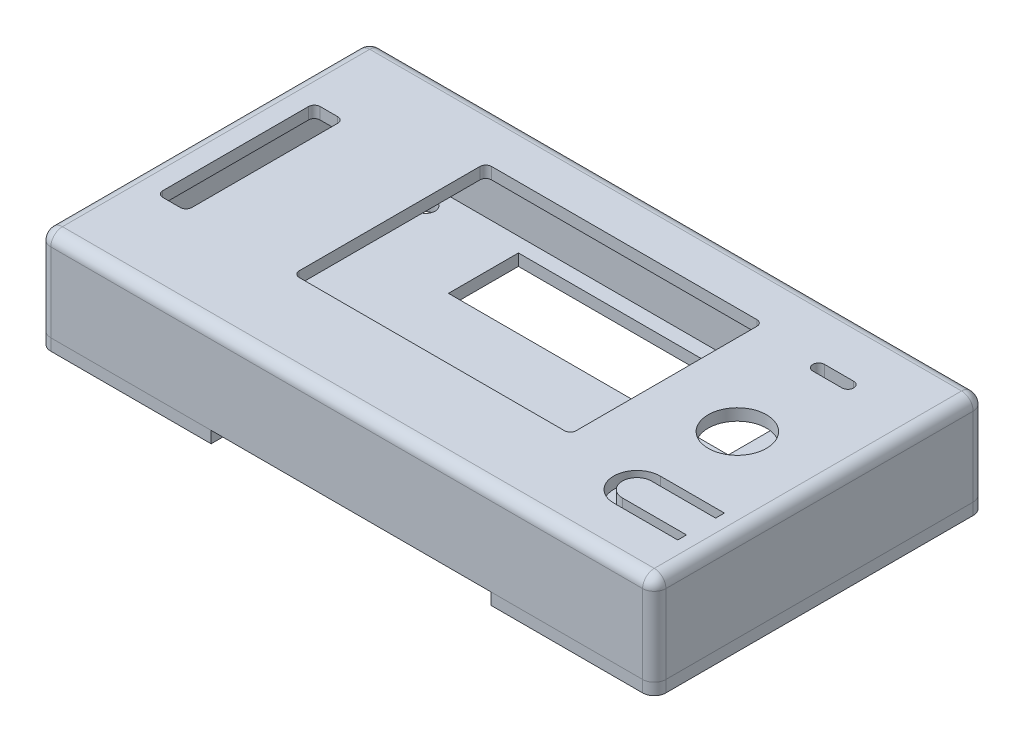
SolidWorks part; units mm, degrees
ref_plane "Alzado" through (0, 0, 0) normal (0, 0, 1) x (1, 0, 0)
ref_plane "Planta" through (0, 0, 0) normal (0, 1, 0) x (1, 0, 0)
ref_plane "Vista lateral" through (0, 0, 0) normal (1, 0, 0) x (0, 0, -1)
sketch "Croquis1" plane through (0, 0, 0) normal (0, 1, 0) x (1, 0, 0)
  line L0 (-2.25, 54.45) -> (103.25, 54.45)
  line L1 (0, 0) -> (101, 0) construction
  line L2 (0, 0) -> (0, 52.2) construction
  line L3 (0, 52.2) -> (101, 52.2) construction
  line L4 (101, 0) -> (101, 52.2) construction
  line L5 (26.6, 45.5) -> (74.1, 45.5)
  line L6 (26.6, 45.5) -> (26.6, 12.5)
  line L7 (26.6, 12.5) -> (74.1, 12.5)
  line L8 (74.1, 45.5) -> (74.1, 12.5)
  line L9 (3, 39.7) -> (8, 39.7)
  line L10 (3, 39.7) -> (3, 12.7)
  line L11 (3, 12.7) -> (8, 12.7)
  line L12 (8, 39.7) -> (8, 12.7)
  line L13 (103.25, -2.25) -> (103.25, 54.45)
  line L14 (-2.25, -2.25) -> (103.25, -2.25)
  line L15 (-2.25, -2.25) -> (-2.25, 54.45)
  line L16 (88.05, 12.48) -> (99.05, 12.48)
  line L17 (88.05, 7.48) -> (99.05, 7.48)
  line L18 (88.05, 5.98) -> (99.05, 5.98)
  line L19 (88.05, 13.98) -> (99.05, 13.98)
  line L20 (99.05, 13.98) -> (99.05, 12.48)
  line L21 (99.05, 7.48) -> (99.05, 5.98)
  line L22 (90.55, 43.65) -> (85.55, 43.65) construction
  line L23 (90.55, 42.65) -> (85.55, 42.65)
  line L24 (90.55, 44.65) -> (85.55, 44.65)
  line L25 (-0.75, -0.75) -> (101.75, -0.75) construction
  line L26 (101.75, -0.75) -> (101.75, 52.95) construction
  line L27 (-0.75, 52.95) -> (101.75, 52.95) construction
  line L28 (-0.75, -0.75) -> (-0.75, 52.95) construction
  circle A0 centre (98.3, 49.5) radius 1.6 construction
  circle A1 centre (98.3, 2.7) radius 1.6 construction
  circle A2 centre (12.3, 49.5) radius 1.6 construction
  circle A3 centre (12.3, 2.7) radius 1.6 construction
  circle A4 centre (88.05, 27.2) radius 5
  circle A5 centre (88.05, 43.65) radius 3 construction
  arc A6 (88.05, 12.48) -> (88.05, 7.48) centre (88.05, 9.98) ccw
  arc A7 (88.05, 13.98) -> (88.05, 5.98) centre (88.05, 9.98) ccw
  arc A8 (90.55, 42.65) -> (90.55, 44.65) centre (90.55, 43.65) ccw
  arc A9 (85.55, 44.65) -> (85.55, 42.65) centre (85.55, 43.65) ccw
  point P41 (88.05, 43.65)
  dimension "D3" = 3.2
  dimension "D6" = 2.7
  dimension "D12" = 10
  dimension "D15" = 6
  dimension "D17" = 5
  dimension "D1" = 52.2
  dimension "D2" = 101
  dimension "D4" = 46.8
  dimension "D5" = 2.7
  dimension "D7" = 86
  dimension "D8" = 47.5
  dimension "D9" = 33
  dimension "D10" = 12.5
  dimension "D11" = 26.9
  dimension "D13" = 12.95
  dimension "D14" = 25
  dimension "D16" = 8.55
  dimension "D18" = 17.22
  dimension "D19" = 27
  dimension "D20" = 5
  dimension "D21" = 12.5
  dimension "D22" = 8
  dimension "D24" = 11
  dimension "D25" = 1.5
  dimension "D26" = 5
  dimension "D27" = 2
  dimension "D23" = 1.5
  dimension "D28" = 0.75
extrude "Saliente-Extruir1" add sketch "Croquis1" along normal blind 2
sketch "Croquis5" plane through (0, 0, 0) normal (0, -1, 0) x (1, 0, 0)
  line L8 (-2.25, 2.25) -> (-2.25, -54.45) construction
  line L9 (-2.25, 2.25) -> (103.25, 2.25) construction
  line L10 (103.25, 2.25) -> (103.25, -54.45) construction
  line L11 (-2.25, -54.45) -> (103.25, -54.45) construction
  line L12 (-2.25, 2.25) -> (-2.25, -54.45)
  line L13 (-2.25, 2.25) -> (103.25, 2.25)
  line L14 (103.25, 2.25) -> (103.25, -54.45)
  line L15 (-2.25, -54.45) -> (103.25, -54.45)
  line L16 (101.75, 0.75) -> (101.75, -52.95) construction
  line L17 (-0.75, 0.75) -> (101.75, 0.75) construction
  line L18 (-0.75, 0.75) -> (-0.75, -52.95) construction
  line L19 (-0.75, -52.95) -> (101.75, -52.95) construction
  line L20 (101.75, 0.75) -> (101.75, -52.95)
  line L21 (-0.75, 0.75) -> (101.75, 0.75)
  line L22 (-0.75, 0.75) -> (-0.75, -52.95)
  line L23 (-0.75, -52.95) -> (101.75, -52.95)
extrude "Saliente-Extruir4" add sketch "Croquis5" along normal blind 13.5
sketch "Croquis6" plane through (0, -13.5, 0) normal (0, -1, 0) x (1, 0, 0)
  line L0 (103.25, 2.25) -> (103.25, -54.45) construction
  line L1 (-2.25, 2.25) -> (103.25, 2.25) construction
  line L2 (-2.25, 2.25) -> (-2.25, -54.45) construction
  line L3 (-2.25, -54.45) -> (103.25, -54.45) construction
  line L4 (103.25, 2.25) -> (103.25, -54.45)
  line L5 (-2.25, 2.25) -> (27.25, 2.25)
  line L6 (-2.25, 2.25) -> (-2.25, -54.45)
  line L7 (-2.25, -54.45) -> (103.25, -54.45)
  line L8 (50.5, 2.25) -> (50.5, -54.45) construction
  line L9 (-0.75, 0.75) -> (-0.75, -52.95) construction
  line L14 (9.45, -48.95) -> (2.45, -48.95)
  line L15 (9.45, -48.95) -> (9.45, -3.95)
  line L16 (9.45, -3.95) -> (2.45, -3.95)
  line L17 (2.45, -48.95) -> (2.45, -3.95)
  line L18 (-0.75, -52.95) -> (101.75, -52.95) construction
  line L19 (103.25, -26.1) -> (-2.25, -26.1) construction
  line L20 (75.25, -50.45) -> (27.25, -50.45)
  line L21 (75.25, -50.45) -> (75.25, -38.45)
  line L22 (75.25, -38.45) -> (27.25, -38.45)
  line L23 (27.25, -50.45) -> (27.25, -38.45)
  line L25 (75.25, 2.25) -> (75.25, -3.75)
  line L26 (75.25, -3.75) -> (27.25, -3.75)
  line L27 (27.25, 2.25) -> (27.25, -3.75)
  line L28 (75.25, 2.25) -> (103.25, 2.25)
  circle A0 centre (98.3, -2.7) radius 1.6 construction
  circle A1 centre (12.3, -49.5) radius 1.6 construction
  circle A2 centre (12.3, -49.5) radius 1.6
  circle A3 centre (98.3, -49.5) radius 1.6 construction
  circle A4 centre (98.3, -2.7) radius 1.6
  circle A7 centre (98.3, -49.5) radius 1.6
  circle A14 centre (12.3, -2.7) radius 1.6 construction
  circle A15 centre (12.3, -2.7) radius 1.6
  circle A16 centre (80.5, -26.1) radius 1.55
  circle A17 centre (20.5, -26.1) radius 1.55
  dimension "D5" = 48
  dimension "D11" = 3.1
  dimension "D1" = 45
  dimension "D2" = 7
  dimension "D3" = 3.2
  dimension "D4" = 4
  dimension "D6" = 12
  dimension "D7" = 2.5
  dimension "D8" = 28
  dimension "D9" = 48
  dimension "D10" = 6
  dimension "D12" = 30
extrude "Saliente-Extruir5" add sketch "Croquis6" along normal blind 2
ref_plane "Plano1" through (0, -13.5, 0) normal (0, -1, 0) x (-1, 0, 0)
sketch "Croquis8" plane through (0, 0, 0) normal (0, -1, 0) x (1, 0, 0)
  line L0 (0, 0) -> (101, 0) construction
  line L2 (9.225, 0.75) -> (9.225, -6.25)
  line L3 (9.225, -6.25) -> (15.375, -6.25)
  line L4 (15.375, 0.75) -> (15.375, -6.25)
  line L5 (101, -26.1) -> (-2.25, -26.1) construction
  line L6 (101, 0) -> (101, -52.2) construction
  line L7 (-2.25, 2.25) -> (-2.25, -54.45) construction
  line L8 (50.5, 0) -> (50.5, -52.2) construction
  line L9 (0, -52.2) -> (101, -52.2) construction
  line L17 (101.75, -6.25) -> (95.6, -6.25)
  line L18 (95.6, 0.75) -> (95.6, -6.25)
  line L23 (101.75, 0.75) -> (101.75, -52.95) construction
  line L24 (-0.75, 0.75) -> (101.75, 0.75) construction
  line L25 (95.6, 0.75) -> (101.75, 0.75)
  line L26 (101.75, 0.75) -> (101.75, -6.25)
  line L27 (9.225, 0.75) -> (15.375, 0.75)
  line L28 (9.225, -52.95) -> (15.375, -52.95)
  line L29 (15.375, -52.95) -> (15.375, -45.95)
  line L30 (9.225, -45.95) -> (15.375, -45.95)
  line L31 (9.225, -52.95) -> (9.225, -45.95)
  line L32 (101.75, -52.95) -> (101.75, -45.95)
  line L33 (95.6, -52.95) -> (101.75, -52.95)
  line L34 (101.75, -45.95) -> (95.6, -45.95)
  line L35 (95.6, -52.95) -> (95.6, -45.95)
  dimension "D1" = 6.15
  dimension "D2" = 7
  dimension "D3" = 3.075
  dimension "D4" = 7
  dimension "D5" = 6.15
extrude "Saliente-Extruir13" add sketch "Croquis8" along normal blind 9
sketch "Croquis9" plane through (0, -9, 0) normal (0, -1, 0) x (1, 0, 0)
  circle A0 centre (12.3, -2.7) radius 2.15
  circle A1 centre (98.3, -2.7) radius 2.15
  circle A2 centre (98.3, -49.5) radius 2.15
  circle A3 centre (12.3, -49.5) radius 2.15
  dimension "D1" = 4.3
extrude "Cortar-Extruir2" cut sketch "Croquis9" against normal blind 3.5
fillet "Redondeo4" radius 2 8 edges at (103.25, -6.75, -54.45) (-2.25, -6.75, -54.45) (-2.25, -6.75, 2.25) (-2.25, 2, -26.1) (50.5, 2, -54.45) (103.25, 2, -26.1) (50.5, 2, 2.25) (103.25, -6.75, 2.25)
split "Partir1" trim tools "Plano1" bodies to split 108 resulting bodies 111 112
fillet "Redondeo6" radius 1 8 edges at (8, 1, -39.7) (3, 1, -39.7) (3, 1, -12.7) (8, 1, -12.7) (26.6, 1, -12.5) (74.1, 1, -12.5) (74.1, 1, -45.5) (26.6, 1, -45.5)
fillet "Redondeo7" radius 1 18 edges at (101.75, -4.5, -6.25) (100.4, 0, -6.25) (95.6, 0, -2.615) (95.6, -4.5, 0.75) (9.225, -4.5, 0.75) (9.225, 0, -2.75) (12.3, 0, -6.25) (15.375, 0, -2.75) (15.375, -4.5, 0.75) (9.225, -4.5, -52.95) (9.225, 0, -49.45) (12.3, 0, -45.95) (15.375, 0, -49.45) (15.375, -4.5, -52.95) (95.6, -4.5, -52.95) (101.75, -4.5, -45.95) (98.675, 0, -45.95) (95.6, 0, -49.45)
sketch "Croquis10" plane through (0, 0, 0) normal (0, -1, 0) x (1, 0, 0)
  circle A0 centre (88.05, -9.98) radius 2.5
extrude "Saliente-Extruir14" add sketch "Croquis10" along normal blind 2 contours A0
